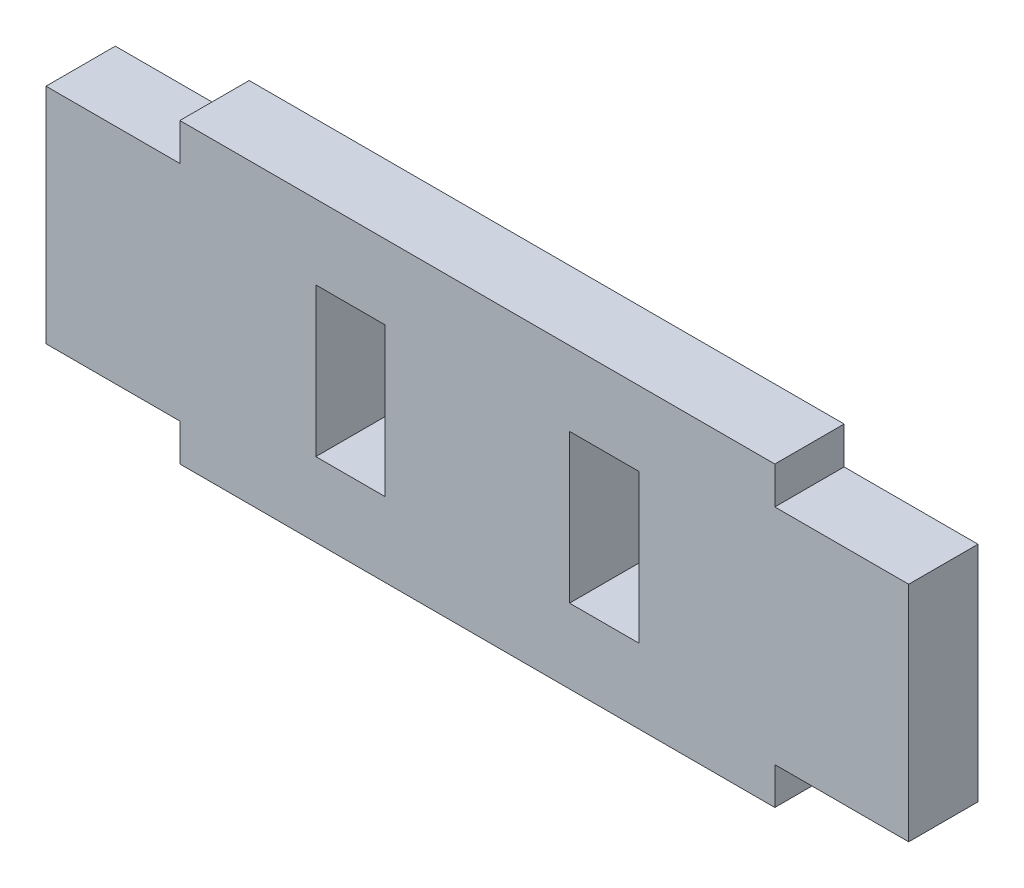
SolidWorks part; units mm, degrees
ref_plane "Front Plane" through (0, 0, 0) normal (0, 0, 1) x (1, 0, 0)
ref_plane "Top Plane" through (0, 0, 0) normal (0, 1, 0) x (1, 0, 0)
ref_plane "Right Plane" through (0, 0, 0) normal (1, 0, 0) x (0, 0, -1)
sketch "Sketch3" plane through (0, 0, 0) normal (0, 0, 1) x (1, 0, 0)
  line L0 (-3.937, 0) -> (3.937, 0) construction
  line L1 (-3.937, 3.175) -> (-3.937, -3.175)
  line L2 (-3.937, -3.175) -> (-6.8961, -3.175)
  line L3 (-6.8961, -3.175) -> (-6.8961, -9.525) construction
  line L4 (-6.8961, -9.525) -> (-9.8552, -9.525) construction
  line L5 (-9.8552, -9.525) -> (-9.8552, 9.525) construction
  line L6 (0, 2.1142) -> (0, -2.8878) construction
  line L7 (-6.8961, 9.525) -> (-9.8552, 9.525) construction
  line L8 (-6.8961, 3.175) -> (-6.8961, 9.525) construction
  line L9 (-3.937, 3.175) -> (-6.8961, 3.175)
  line L10 (3.937, 3.175) -> (6.8961, 3.175)
  line L11 (6.8961, 3.175) -> (6.8961, 9.525) construction
  line L12 (6.8961, 9.525) -> (9.8552, 9.525) construction
  line L13 (9.8552, -9.525) -> (9.8552, 9.525) construction
  line L14 (6.8961, -9.525) -> (9.8552, -9.525) construction
  line L15 (6.8961, -3.175) -> (6.8961, -9.525) construction
  line L16 (3.937, -3.175) -> (6.8961, -3.175)
  line L17 (3.937, 3.175) -> (3.937, -3.175)
  line L18 (-6.8961, 3.175) -> (-6.8961, -3.175)
  line L19 (-12.7, 6.35) -> (12.7, 6.35)
  line L20 (-12.7, 6.35) -> (-12.7, 4.7625)
  line L21 (-12.7, -6.35) -> (12.7, -6.35)
  line L22 (12.7, 6.35) -> (12.7, 4.7625)
  line L23 (-12.7, 6.35) -> (12.7, -6.35) construction
  line L24 (-12.7, -6.35) -> (12.7, 6.35) construction
  line L25 (6.8961, 3.175) -> (6.8961, -3.175)
  line L26 (-12.7, 4.7625) -> (-18.415, 4.7625)
  line L27 (12.7, 4.7625) -> (18.415, 4.7625)
  line L29 (12.7, -4.7625) -> (18.415, -4.7625)
  line L30 (18.415, 4.7625) -> (18.415, -4.7625)
  line L31 (-18.415, 4.7625) -> (-18.415, -4.7625)
  line L32 (-12.7, -4.7625) -> (-18.415, -4.7625)
  line L33 (12.7, -4.7625) -> (12.7, -6.35)
  line L34 (-12.7, -4.7625) -> (-12.7, -6.35)
  point P21 (0, 0)
  point P30 (18.415, 0)
  dimension "D1" = 7.874
  dimension "D2" = 9.525
  dimension "D3" = 2.9591
  dimension "D4" = 6.35
  dimension "D5" = 2.9591
  dimension "D6" = 12.7
  dimension "D7" = 25.4
  dimension "D8" = 9.525
  dimension "D9" = 5.715
extrude "Boss-Extrude1" add sketch "Sketch3" along normal mid plane 2.9591
